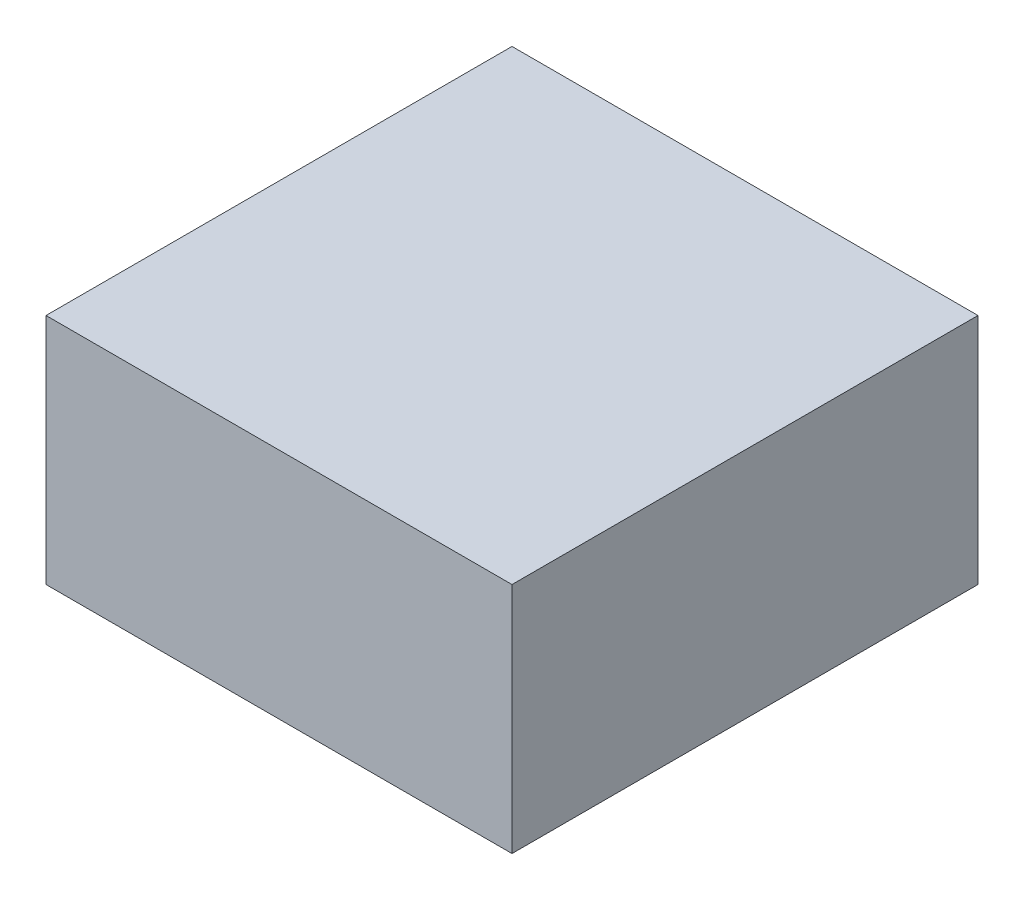
SolidWorks part; units mm, degrees
ref_plane "Front Plane" through (0, 0, 0) normal (0, 0, 1) x (1, 0, 0)
ref_plane "Top Plane" through (0, 0, 0) normal (0, 1, 0) x (1, 0, 0)
ref_plane "Right Plane" through (0, 0, 0) normal (1, 0, 0) x (0, 0, -1)
sketch "Sketch1" plane through (0, 0, 0) normal (0, 1, 0) x (1, 0, 0)
  line L1 (0, 0) -> (1.524, 0)
  line L2 (0, 0) -> (0, 1.524)
  line L3 (0, 1.524) -> (1.524, 1.524)
  line L4 (1.524, 0) -> (1.524, 1.524)
  dimension "D1" = 1.524
  dimension "D2" = 1.524
extrude "Boss-Extrude1" add sketch "Sketch1" along normal blind 0.762
